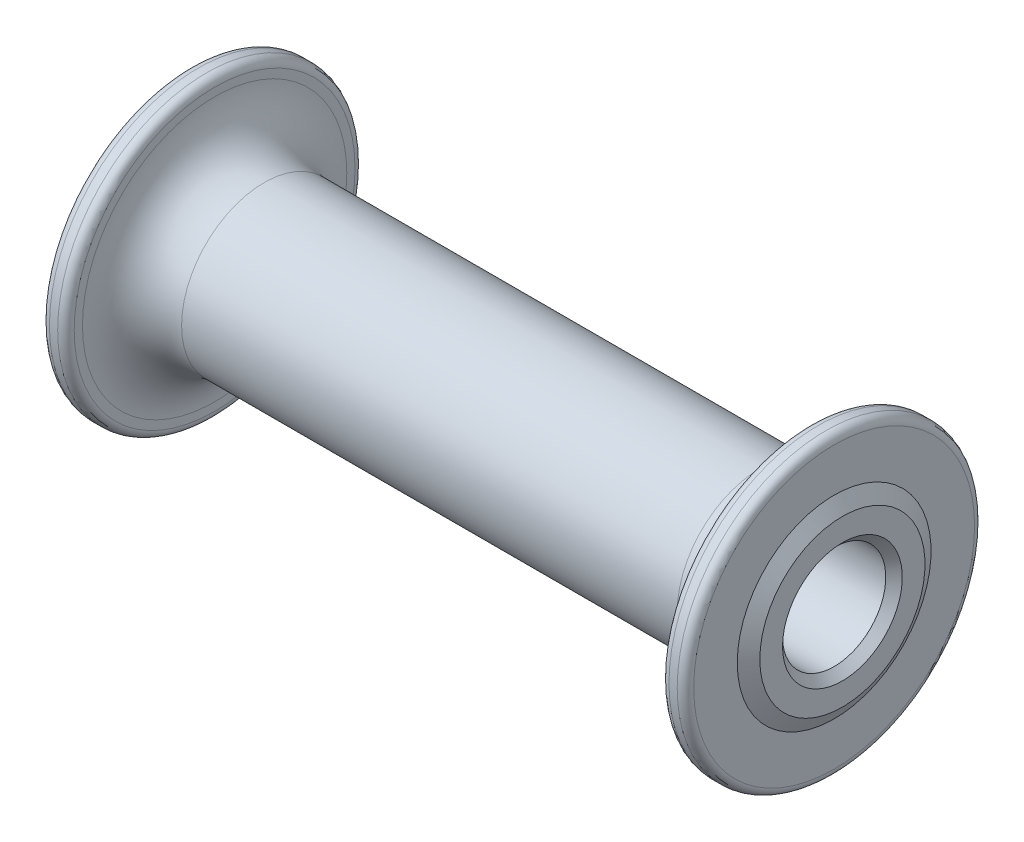
SolidWorks part; units mm, degrees
ref_plane "Plane1" through (0, 0, 0) normal (0, 0, 1) x (1, 0, 0)
ref_plane "Plane2" through (0, 0, 0) normal (0, 1, 0) x (1, 0, 0)
ref_plane "Plane3" through (0, 0, 0) normal (1, 0, 0) x (0, 0, -1)
sketch "Sketch1" plane through (0, 0, 0) normal (0, 0, 1) x (1, 0, 0)
  line L0 (0, 0) -> (53, 0) construction
  line L1 (40, 6.25) -> (40, 10)
  line L2 (40, 10) -> (39, 11.7321)
  line L3 (39, 11.7321) -> (39, 17)
  line L4 (38, 18) -> (37, 18)
  line L5 (36, 17) -> (36, 16)
  line L6 (30, 10) -> (-30, 10)
  line L7 (40, 6.25) -> (-40, 6.25)
  line L8 (0, 0) -> (0, 10) construction
  line L9 (-36, 17) -> (-36, 16)
  line L10 (-38, 18) -> (-37, 18)
  line L11 (-39, 11.7321) -> (-39, 17)
  line L12 (-40, 10) -> (-39, 11.7321)
  line L13 (-40, 6.25) -> (-40, 10)
  line L14 (0, 10) -> (0, 35) construction
  arc A0 (36, 16) -> (30, 10) centre (30, 16) cw
  arc A1 (-36, 16) -> (-30, 10) centre (-30, 16) ccw
  arc A2 (37, 18) -> (36, 17) centre (37, 17) ccw
  arc A3 (-36, 17) -> (-37, 18) centre (-37, 17) ccw
  arc A4 (39, 17) -> (38, 18) centre (38, 17) ccw
  arc A5 (-38, 18) -> (-39, 17) centre (-38, 17) ccw
  circle A6 centre (-26, 18.5) radius 8.5 construction
  circle A7 centre (-9, 18.5) radius 8.5 construction
  circle A8 centre (26, 18.5) radius 8.5 construction
  circle A9 centre (9, 18.5) radius 8.5 construction
  point P17 (0, 6.25)
  point P23 (36, 18)
  point P26 (-36, 18)
  point P29 (39, 18)
  point P32 (-39, 18)
  dimension "D5" = 6
  dimension "D11" = 1
  dimension "D13" = 17
  dimension "D15" = 34
  dimension "D1" = 1
  dimension "D2" = 20
  dimension "D3" = 12.5
  dimension "D4" = 30
  dimension "D6" = 72
  dimension "D7" = 20
  dimension "D8" = 36
  dimension "D9" = 4
  dimension "D12" = 80
  dimension "D14" = 18
revolve "Revolve1" add sketch "Sketch1" angle 360 about L0
chamfer "Kantreifning1" distance 1 angle 45 2 edges at (-40, 0, 6.25) (40, 0, 6.25)
